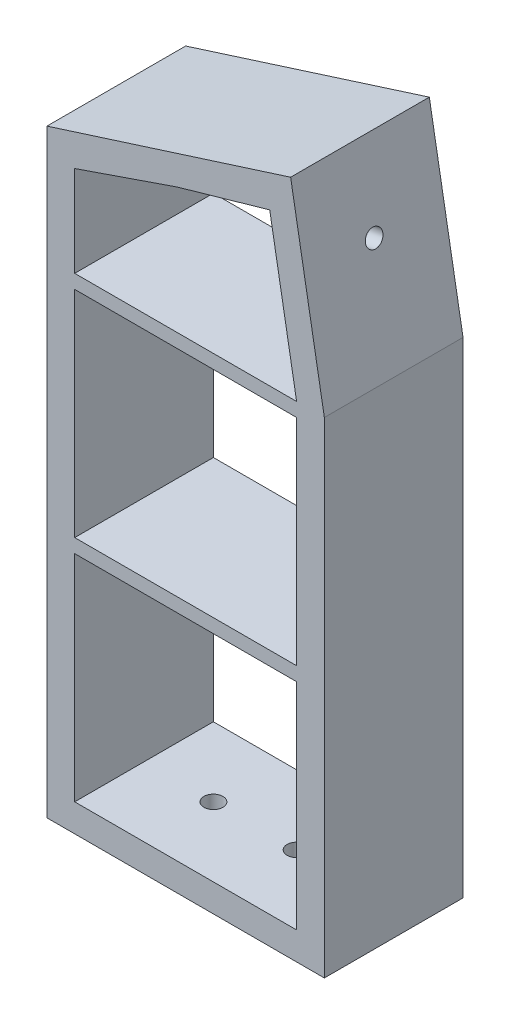
SolidWorks part; units mm, degrees
ref_plane "Front Plane" through (0, 0, 0) normal (0, 0, 1) x (1, 0, 0)
ref_plane "Top Plane" through (0, 0, 0) normal (0, 1, 0) x (1, 0, 0)
ref_plane "Right Plane" through (0, 0, 0) normal (1, 0, 0) x (0, 0, -1)
sketch "Sketch2" plane through (0, 0, 0) normal (0, 0, 1) x (1, 0, 0)
  line L6 (-40.869, 215.9795) -> (-40.869, 0)
  line L8 (-40.869, 0) -> (59.131, 0)
  line L10 (-40.869, 215.9795) -> (59.131, 0) construction
  line L11 (-40.869, 0) -> (59.131, 215.9795) construction
  line L12 (59.131, 0) -> (59.131, 175)
  line L13 (59.131, 175) -> (46.9756, 243.9365)
  line L14 (59.131, 175) -> (59.131, 266.0824) construction
  line L15 (46.9756, 243.9365) -> (-40.869, 215.9795)
  line L16 (-40.869, 107.9897) -> (-30.869, 107.9897) construction
  line L17 (3.0533, 229.958) -> (6.086, 220.4289) construction
  line L18 (59.131, 87.5) -> (49.131, 87.5) construction
  line L19 (0, 0) -> (0, 10) construction
  line L20 (0, 10) -> (49.131, 10)
  line L21 (49.131, 10) -> (49.131, 87.5)
  line L22 (49.131, 87.5) -> (49.131, 175)
  line L23 (53.0533, 209.4683) -> (43.2052, 207.7318) construction
  line L24 (49.131, 175) -> (39.4404, 229.958)
  line L25 (39.4404, 229.958) -> (6.086, 220.4289)
  line L26 (6.086, 220.4289) -> (-30.869, 207.7318)
  line L27 (-30.869, 207.7318) -> (-30.869, 107.9897)
  line L28 (-30.869, 107.9897) -> (-30.869, 10)
  line L29 (-30.869, 10) -> (0, 10)
  point P1 (9.131, 107.9897)
  dimension "D2" = 100
  dimension "D3" = 10
  dimension "D4" = 6.086
  dimension "D5" = 9.131
  dimension "D6" = 39.4404
  dimension "D7" = 46.9756
extrude "Boss-Extrude1" add sketch "Sketch2" along normal blind 50
sketch "Sketch4" plane through (87.2747, 15.3889, 0) normal (0.9848, 0.1736, 0) x (0, 0, -1)
  line L0 (-25, 162.0734) -> (-25, 202.6904) construction
  line L1 (-50, 162.0734) -> (0, 162.0734) construction
  line L2 (-50, 232.0734) -> (0, 232.0734) construction
  circle A0 centre (-25, 202.6904) radius 3.15
  dimension "D1" = 6.3
  dimension "D2" = 29.383
extrude "Cut-Extrude1" cut sketch "Sketch4" against normal blind 10
sketch "Sketch10" plane through (0, 10, 0) normal (0, 1, 0) x (1, 0, 0)
  line L0 (49.131, -25) -> (24.131, -25) construction
  line L1 (-30.869, -50) -> (-30.869, 0) construction
  line L3 (-30.869, -25) -> (-5.8513, -25) construction
  line L4 (49.131, -50) -> (49.131, 0) construction
  circle A0 centre (-5.8513, -25) radius 3.425
  circle A1 centre (24.131, -25) radius 3.425
  dimension "D1" = 6.85
  dimension "D2" = 6.85
  dimension "D3" = 25.0177
  dimension "D4" = 55
extrude "Cut-Extrude5" cut sketch "Sketch10" against normal blind 10
sketch "Sketch12" plane through (0, 0, 50) normal (0, 0, 1) x (1, 0, 0)
  line L0 (49.131, 10) -> (49.131, 92.5) construction
  line L1 (49.131, 10) -> (49.131, 175) construction
  line L2 (49.131, 92.5) -> (49.131, 175) construction
  line L3 (-30.869, 207.7318) -> (-30.869, 10) construction
  line L4 (49.131, 175) -> (-30.869, 175)
  line L5 (49.131, 175) -> (49.131, 170)
  line L6 (49.131, 170) -> (-30.869, 170)
  line L7 (-30.869, 175) -> (-30.869, 170)
  line L9 (49.131, 92.5) -> (-30.869, 92.5)
  line L10 (49.131, 92.5) -> (49.131, 87.5)
  line L11 (49.131, 87.5) -> (-30.869, 87.5)
  line L12 (-30.869, 92.5) -> (-30.869, 87.5)
  dimension "D1" = 5
  dimension "D2" = 5
  dimension "D3" = 165
  dimension "D4" = 82.5
extrude "Boss-Extrude2" add sketch "Sketch12" against normal blind 50
